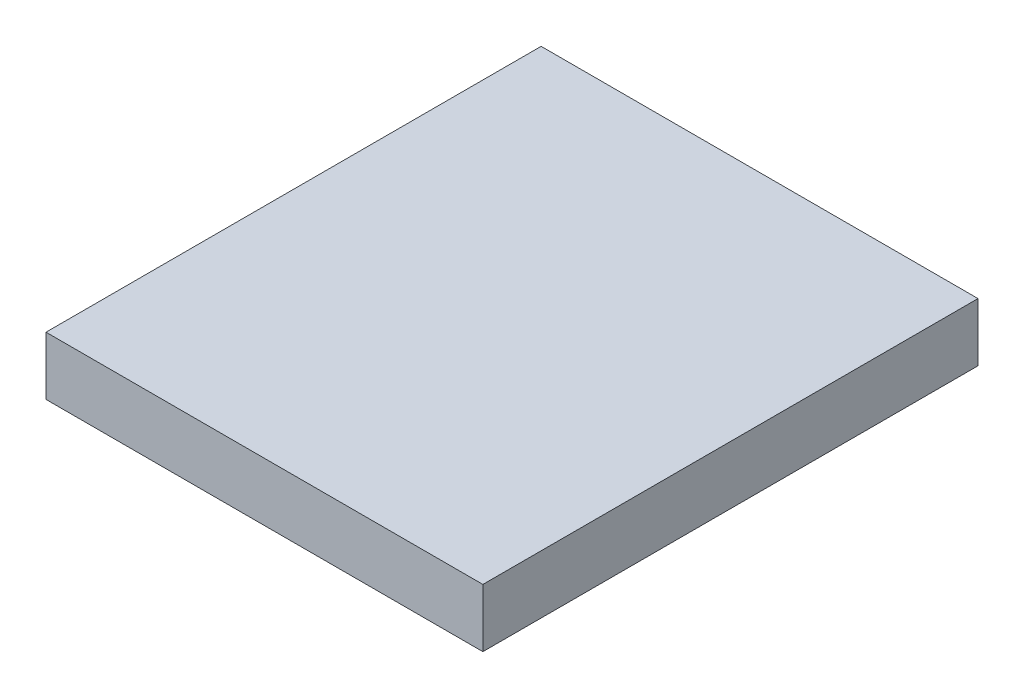
SolidWorks part; units mm, degrees
material "Oak"
ref_plane "Front Plane" through (0, 0, 0) normal (0, 0, 1) x (1, 0, 0)
ref_plane "Top Plane" through (0, 0, 0) normal (0, 1, 0) x (1, 0, 0)
ref_plane "Right Plane" through (0, 0, 0) normal (1, 0, 0) x (0, 0, -1)
sketch "Sketch1" plane through (0, 0, 0) normal (0, 1, 0) x (1, 0, 0)
  line L1 (-95.25, 107.95) -> (95.25, 107.95)
  line L2 (-95.25, 107.95) -> (-95.25, -107.95)
  line L3 (-95.25, -107.95) -> (95.25, -107.95)
  line L4 (95.25, 107.95) -> (95.25, -107.95)
  line L5 (-95.25, 107.95) -> (95.25, -107.95) construction
  line L6 (-95.25, -107.95) -> (95.25, 107.95) construction
  point P0 (0, 0)
  dimension "D1" = 190.5
  dimension "D2" = 215.9
extrude "Boss-Extrude1" add sketch "Sketch1" along normal blind 25.4
